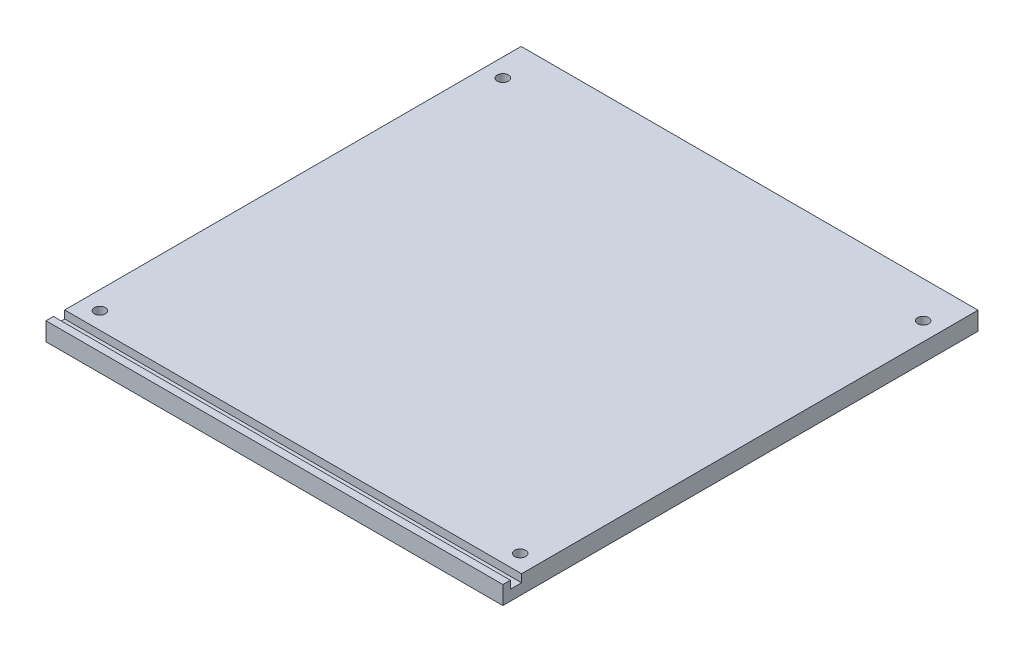
SolidWorks part; units mm, degrees
ref_plane "Alzado" through (0, 0, 0) normal (0, 0, 1) x (1, 0, 0)
ref_plane "Planta" through (0, 0, 0) normal (0, 1, 0) x (1, 0, 0)
ref_plane "Vista lateral" through (0, 0, 0) normal (1, 0, 0) x (0, 0, -1)
sketch "Croquis1" plane through (0, 0, 0) normal (0, 1, 0) x (1, 0, 0)
  line L1 (-125, 130) -> (125, 130)
  line L2 (-125, 130) -> (-125, -130)
  line L3 (-125, -130) -> (125, -130)
  line L4 (125, 130) -> (125, -130)
  line L5 (-125, 130) -> (125, -130) construction
  line L6 (-125, -130) -> (125, 130) construction
  point P0 (0, 0)
  dimension "D1" = 260
  dimension "D2" = 250
extrude "Saliente-Extruir1" add sketch "Croquis1" along normal blind 10
sketch "Croquis4" plane through (-125, 0, 0) normal (-1, 0, 0) x (0, 0, 1)
  line L0 (130, 0) -> (130, 10) construction
  line L1 (130, 10) -> (116.302, 10) construction
  line L2 (120.0324, 6.8172) -> (120.5936, 10) construction
  line L3 (125.6707, 10) -> (124.9564, 5.949) construction
  line L4 (124.9564, 5.949) -> (120.0324, 6.8172) construction
  line L5 (125.6707, 10) -> (125.6707, 5.949) construction
  line L6 (120.0324, 10) -> (120.0324, 5.699) construction
  line L7 (119.7824, 10) -> (125.9207, 10)
  line L8 (120.0324, 5.949) -> (125.6707, 5.949) construction
  line L9 (119.7824, 10) -> (119.7824, 5.699)
  line L10 (125.9207, 10) -> (125.9207, 5.699)
  line L11 (119.7824, 5.699) -> (125.9207, 5.699)
  line L12 (120.0324, 5.699) -> (125.6707, 5.699) construction
  line L13 (125.9207, 10) -> (125.9207, 5.949) construction
  line L15 (120.0324, 10) -> (120.0324, 1.2534) construction
  line L16 (119.7824, 10) -> (119.7824, 1.2534) construction
  dimension "D1" = 0.25
  dimension "D2" = 0.25
  dimension "D3" = 0.25
extrude "Cortar-Extruir1" cut sketch "Croquis4" against normal up to next
sketch "Croquis5" plane through (0, 0, 0) normal (0, -1, 0) x (1, 0, 0)
  line L0 (125, -130) -> (115, -110) construction
  line L1 (115, -110) -> (115, -130) construction
  line L2 (115, -110) -> (125, -109.9186) construction
  line L3 (115, -110) -> (115, 110.5302) construction
  line L4 (115, 110.5302) -> (-115, 110.5302) construction
  line L5 (-115, 110.5302) -> (-115, -110) construction
  line L6 (-115, -110) -> (115, -110) construction
  circle A1 centre (-115, 110.5302) radius 3
  circle A2 centre (115, 110.5302) radius 3
  circle A6 centre (-115, -110) radius 3
  circle A7 centre (115, -110) radius 3
extrude "Cortar-Extruir2" cut sketch "Croquis5" against normal up to next
